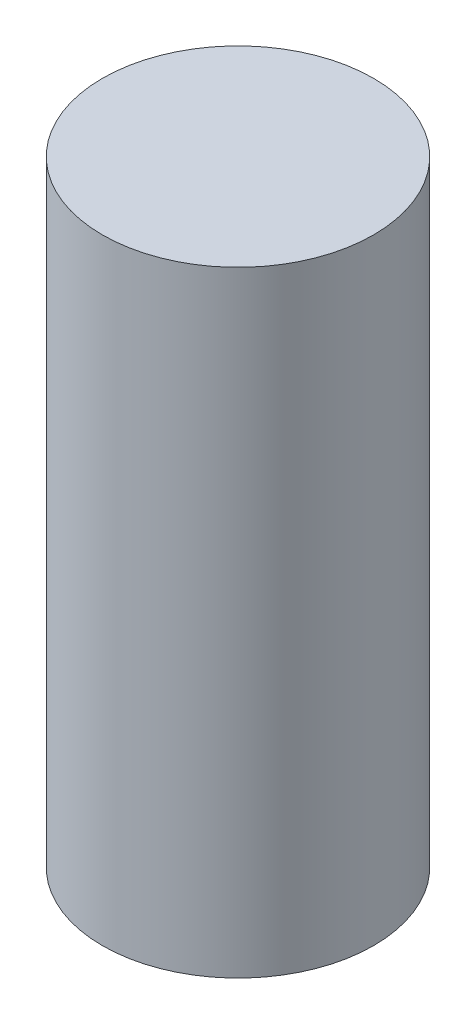
SolidWorks part; units mm, degrees
ref_plane "Front Plane" through (0, 0, 0) normal (0, 0, 1) x (1, 0, 0)
ref_plane "Top Plane" through (0, 0, 0) normal (0, 1, 0) x (1, 0, 0)
ref_plane "Right Plane" through (0, 0, 0) normal (1, 0, 0) x (0, 0, -1)
sketch "Sketch1" plane through (0, 0, 0) normal (0, 1, 0) x (1, 0, 0)
  circle A0 centre (0, 0) radius 282.575
  dimension "D1" = 565.15
extrude "Boss-Extrude1" add sketch "Sketch1" along normal blind 1282.7
